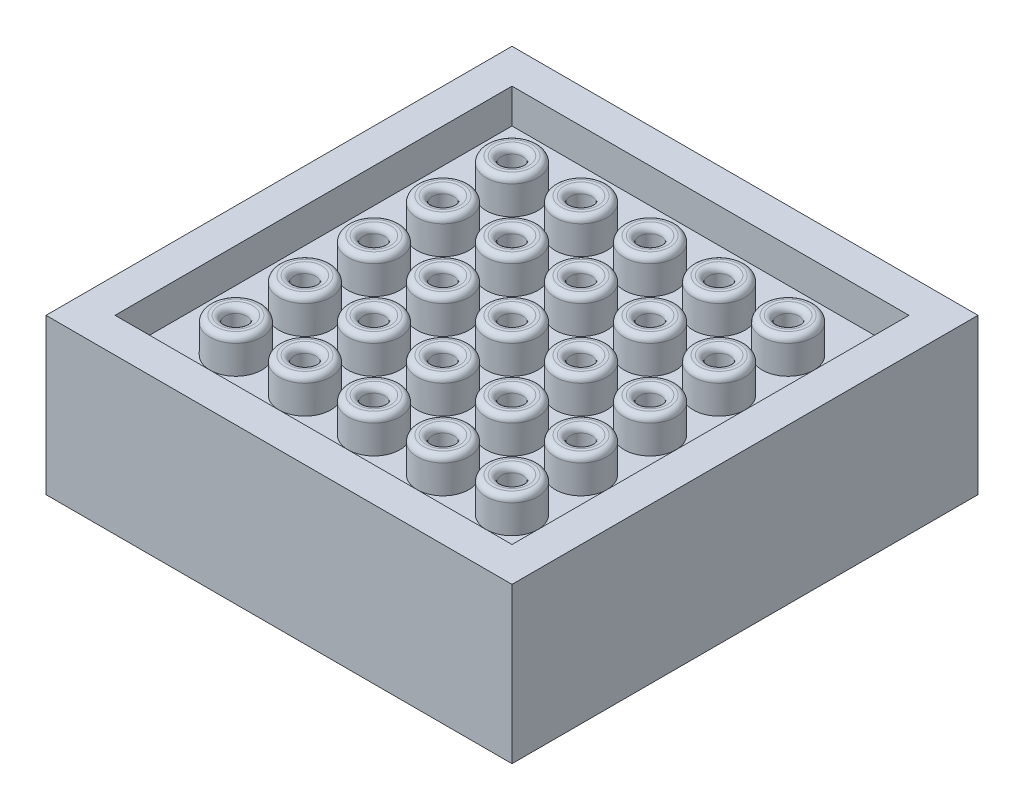
SolidWorks part; units mm, degrees
ref_plane "Front Plane" through (0, 0, 0) normal (0, 0, 1) x (1, 0, 0)
ref_plane "Top Plane" through (0, 0, 0) normal (0, 1, 0) x (1, 0, 0)
ref_plane "Right Plane" through (0, 0, 0) normal (1, 0, 0) x (0, 0, -1)
sketch "Sketch1" plane through (0, 0, 0) normal (0, 1, 0) x (1, 0, 0)
  line L0 (-13.5, 13.5) -> (13.5, 13.5)
  line L1 (-11.5, -11.5) -> (11.5, -11.5)
  line L2 (-11.5, -11.5) -> (-11.5, 11.5)
  line L3 (-11.5, 11.5) -> (11.5, 11.5)
  line L4 (11.5, -11.5) -> (11.5, 11.5)
  line L5 (-11.5, -11.5) -> (11.5, 11.5) construction
  line L6 (-11.5, 11.5) -> (11.5, -11.5) construction
  line L7 (13.5, -13.5) -> (13.5, 13.5)
  line L8 (-13.5, -13.5) -> (13.5, -13.5)
  line L9 (-13.5, -13.5) -> (-13.5, 13.5)
  point P0 (0, 0)
  dimension "D1" = 23
  dimension "D2" = 2
extrude "Boss-Extrude1" add sketch "Sketch1" along normal blind 2
sketch "Sketch2" plane through (0, 0, 0) normal (0, -1, 0) x (1, 0, 0)
  line L1 (-13.5, 13.5) -> (13.5, 13.5)
  line L2 (-13.5, 13.5) -> (-13.5, -13.5)
  line L3 (-13.5, -13.5) -> (13.5, -13.5)
  line L4 (13.5, 13.5) -> (13.5, -13.5)
  line L5 (-13.5, 13.5) -> (13.5, -13.5) construction
  line L6 (-13.5, -13.5) -> (13.5, 13.5) construction
  point P0 (0, 0)
extrude "Boss-Extrude2" add sketch "Sketch2" along normal blind 2
sketch "Sketch3" plane through (0, -2, 0) normal (0, -1, 0) x (1, 0, 0)
  line L0 (-11.5, 11.5) -> (11.5, 11.5)
  line L1 (-13.5, -13.5) -> (13.5, -13.5)
  line L2 (-13.5, -13.5) -> (-13.5, 13.5)
  line L3 (-13.5, 13.5) -> (13.5, 13.5)
  line L4 (13.5, -13.5) -> (13.5, 13.5)
  line L5 (-13.5, -13.5) -> (13.5, 13.5) construction
  line L6 (-13.5, 13.5) -> (13.5, -13.5) construction
  line L7 (11.5, -11.5) -> (11.5, 11.5)
  line L8 (-11.5, -11.5) -> (11.5, -11.5)
  line L9 (-11.5, -11.5) -> (-11.5, 11.5)
  point P0 (0, 0)
  dimension "D1" = 2
extrude "Boss-Extrude3" add sketch "Sketch3" along normal blind 5
sketch "Sketch6" plane through (0, 0, 0) normal (0, 1, 0) x (1, 0, 0)
  line L0 (11.5, -11.5) -> (11.5, 11.5) construction
  line L1 (11.5, 11.5) -> (-11.5, 11.5) construction
  circle A0 centre (8, 8) radius 1.5
  dimension "D2" = 3
  dimension "D1" = 3.5
  dimension "D3" = 3.5
extrude "Boss-Extrude5" add sketch "Sketch6" along normal blind 2
sketch "Sketch7" plane through (0, 2, 0) normal (0, 1, 0) x (1, 0, 0)
  circle A0 centre (8, 8) radius 0.625
  dimension "D1" = 1.25
extrude "Cut-Extrude2" cut sketch "Sketch7" against normal up to next (4 mm away)
fillet "Fillet3" radius 0.35 2 edges at (8, 2, -6.5) (8, 2, -7.375)
pattern_linear "LPattern1" count 5 spacing 4 along (0, 0, 1) count 5 spacing 4 along (-1, 0, 0) of "Boss-Extrude5", "Cut-Extrude2", "Fillet3"
equation "\"D3@Sketch6\"=\"D1@Sketch6\""
